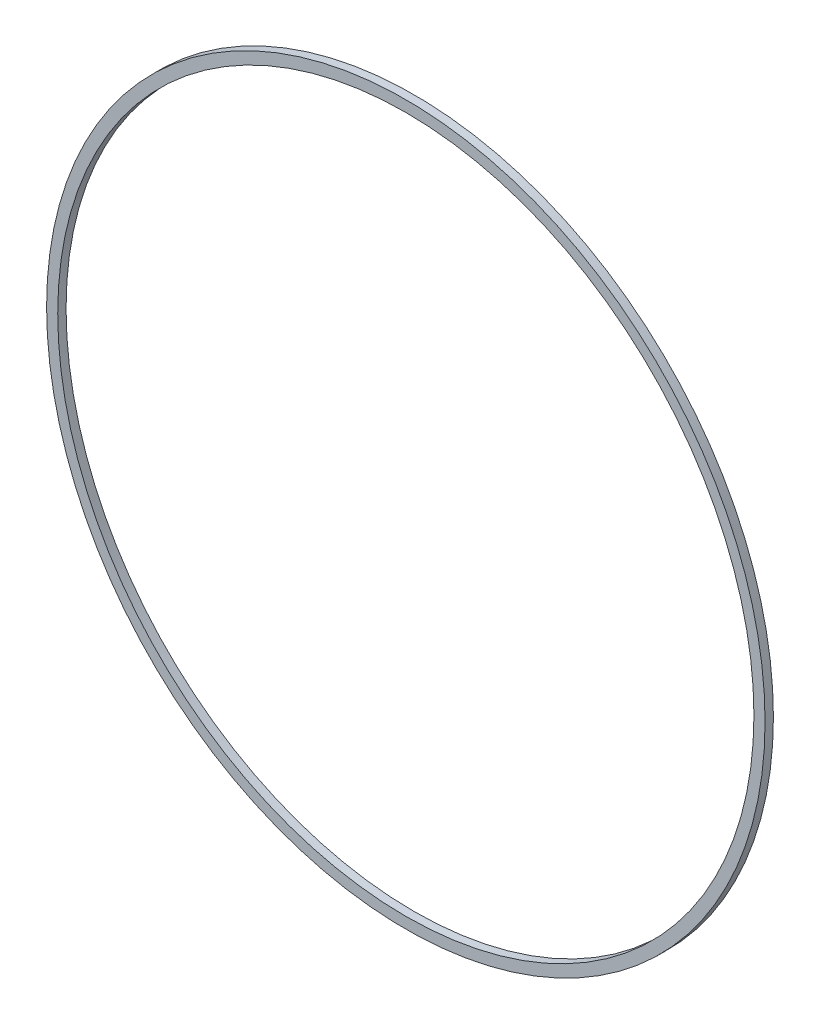
SolidWorks part; units mm, degrees
ref_plane "Alzado" through (0, 0, 0) normal (0, 0, 1) x (1, 0, 0)
ref_plane "Planta" through (0, 0, 0) normal (0, 1, 0) x (1, 0, 0)
ref_plane "Vista lateral" through (0, 0, 0) normal (1, 0, 0) x (0, 0, -1)
sketch "Croquis1" plane through (0, 0, 0) normal (0, 0, 1) x (1, 0, 0)
  circle A0 centre (0, 0) radius 258
  circle A1 centre (0, 0) radius 250
  dimension "D1" = 500
  dimension "D2" = 8
extrude "Saliente-Extruir1" add sketch "Croquis1" along normal blind 6
